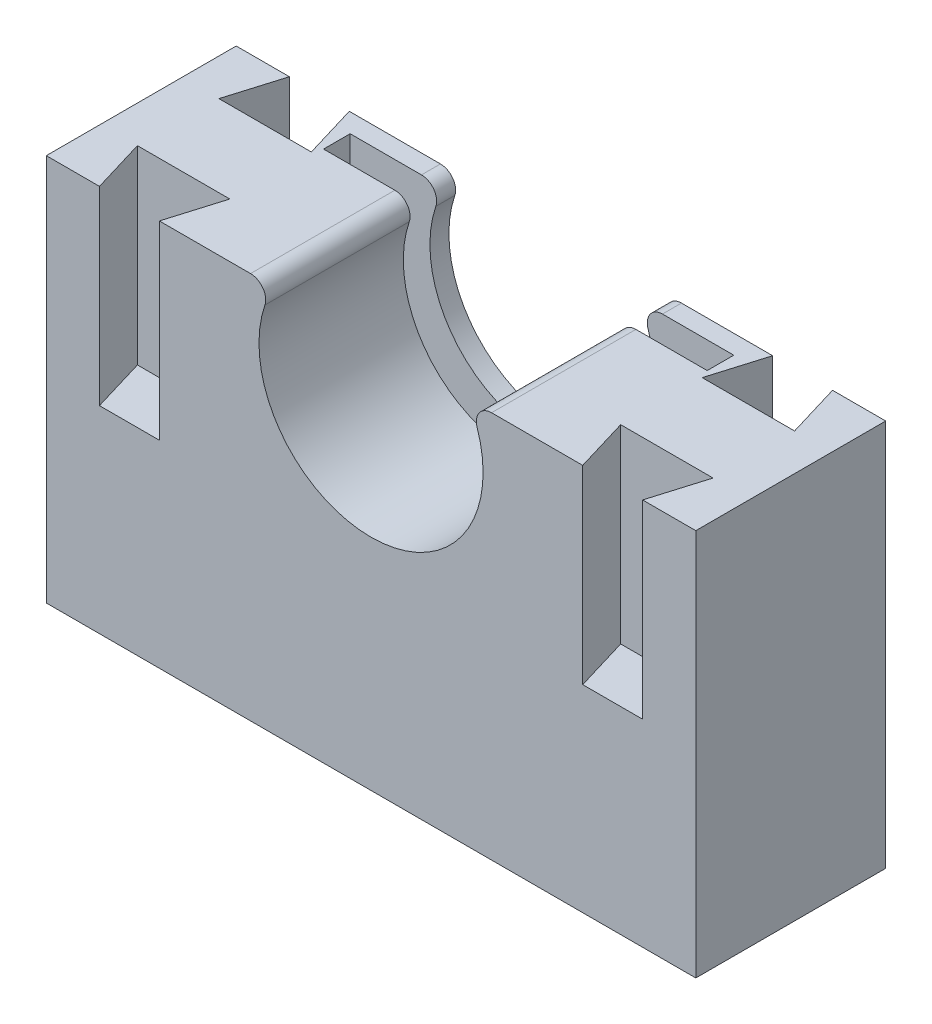
SolidWorks part; units mm, degrees
ref_plane "Front Plane" through (0, 0, 0) normal (0, 0, 1) x (1, 0, 0)
ref_plane "Top Plane" through (0, 0, 0) normal (0, 1, 0) x (1, 0, 0)
ref_plane "Right Plane" through (0, 0, 0) normal (1, 0, 0) x (0, 0, -1)
sketch "Sketch2" plane through (0, 0, 0) normal (0, 0, 1) x (1, 0, 0)
  line L0 (11.1505, 5.8899) -> (11.1505, -22.9851) construction
  line L1 (53.9005, 28.0149) -> (27.0147, 28.0149)
  line L2 (53.9005, 28.0149) -> (53.9005, -22.9851)
  line L3 (53.9005, -22.9851) -> (-31.5995, -22.9851)
  line L4 (-31.5995, 28.0149) -> (-31.5995, -22.9851)
  line L5 (-31.5995, 2.5149) -> (53.9005, 2.5149) construction
  line L6 (-4.7137, 28.0149) -> (-31.5995, 28.0149)
  line L7 (11.1505, 20.6399) -> (11.1505, -22.9851) construction
  line L8 (11.1505, 20.6399) -> (25.1204, 25.3731) construction
  line L9 (-3.5995, 20.6399) -> (25.9005, 20.6399) construction
  arc A0 (-2.8194, 25.3731) -> (25.1204, 25.3731) centre (11.1505, 20.6399) ccw
  arc A1 (-4.7137, 28.0149) -> (-2.8194, 25.3731) centre (-4.7137, 26.0149) cw
  arc A2 (27.0147, 28.0149) -> (25.1204, 25.3731) centre (27.0147, 26.0149) ccw
  dimension "D4" = 2
  dimension "D5" = 29.5
  dimension "D3" = 2
  dimension "D1" = 85.5
  dimension "D2" = 51
extrude "Boss-Extrude1" add sketch "Sketch2" along normal blind 25
sketch "Sketch5" plane through (0, 0, 25) normal (0, 0, 1) x (1, 0, 0)
  line L0 (11.1505, 5.8899) -> (11.1505, 1.4899) construction
  line L1 (-31.5995, -22.9851) -> (53.9005, -22.9851) construction
  line L2 (11.1505, 5.8899) -> (11.1505, 1.4899)
  line L3 (11.1505, -7.3101) -> (11.1505, -22.9851) construction
  arc A0 (-2.8194, 25.3731) -> (25.1204, 25.3731) centre (11.1505, 20.6399) ccw construction
  circle A1 centre (11.1505, -2.9101) radius 4.4
  dimension "D2" = 8.8
  dimension "D1" = 8.8
extrude "Cut-Extrude3" cut sketch "Sketch5" along normal blind 4.8 from surface at -25 contours A1 starting at face at (11.1505, 12.2907, 0)
sketch "Sketch6" plane through (0, 28.0149, 0) normal (0, 1, 0) x (1, 0, 0)
  line L0 (-24.5995, 0) -> (-26.7385, -7.1363)
  line L1 (-4.7137, 0) -> (-31.5995, 0) construction
  line L2 (-26.7385, -7.1363) -> (-14.5747, -7.1363)
  line L3 (-14.5747, -7.1363) -> (-16.7137, 0)
  line L4 (-31.5995, 0) -> (-24.5995, 0)
  line L5 (-16.7137, 0) -> (-4.7137, 0)
  line L6 (-31.5995, -25) -> (-24.5995, -25)
  line L7 (-4.7137, -25) -> (-31.5995, -25) construction
  line L8 (-24.5995, -25) -> (-26.7391, -17.8638)
  line L9 (-26.7391, -17.8638) -> (-14.5741, -17.8638)
  line L10 (-14.5741, -17.8638) -> (-16.7137, -25)
  line L11 (-16.7137, -25) -> (-4.7137, -25)
  line L12 (53.9005, 0) -> (46.9005, 0)
  line L13 (46.9005, 0) -> (49.0401, -7.1362)
  line L14 (49.0401, -7.1362) -> (36.8751, -7.1362)
  line L15 (36.8751, -7.1362) -> (39.0147, 0)
  line L16 (53.9005, 0) -> (27.0147, 0) construction
  line L17 (39.0147, 0) -> (27.0147, 0)
  line L18 (27.0147, -25) -> (39.0147, -25)
  line L19 (53.9005, -25) -> (27.0147, -25) construction
  line L20 (39.0147, -25) -> (36.8751, -17.8638)
  line L21 (36.8751, -17.8638) -> (49.0401, -17.8638)
  line L22 (49.0401, -17.8638) -> (46.9005, -25)
  line L23 (46.9005, -25) -> (53.9005, -25)
  line L24 (-31.5995, 0) -> (-31.5995, -25)
  line L27 (53.9005, 0) -> (53.9005, -25)
  line L28 (-4.7137, 0) -> (27.0147, 0)
  line L29 (27.0147, -25) -> (-4.7137, -25)
  dimension "D1" = 7
  dimension "D2" = 12
  dimension "D3" = 7.45
  dimension "D4" = 7.45
  dimension "D5" = 106.685
  dimension "D6" = 12.1639
  dimension "D7" = 7
  dimension "D8" = 12
  dimension "D9" = 7.45
  dimension "D10" = 7.45
  dimension "D11" = 106.69
  dimension "D12" = 12
  dimension "D13" = 7
  dimension "D14" = 7.45
  dimension "D15" = 7.45
  dimension "D16" = 106.69
  dimension "D17" = 12.165
  dimension "D18" = 12.165
  dimension "D19" = 12
  dimension "D20" = 7
  dimension "D21" = 7.45
  dimension "D22" = 106.69
  dimension "D23" = 7.45
extrude "Cut-Extrude4" cut sketch "Sketch6" against normal blind 25 flip side to cut
ref_plane "Plane1" through (0, 0, 2.5) normal (0, 0, -1) x (-1, 0, 0)
sketch "Sketch8" plane through (0, 0, 2.5) normal (0, 0, -1) x (-1, 0, 0)
  line L0 (-27.0147, 28.0149) -> (4.7137, 28.0149) construction
  line L1 (-11.1505, 28.0149) -> (-11.1505, -7.3101) construction
  line L2 (-36.4005, 2.9448) -> (14.0995, 2.9448)
  line L3 (-36.4005, 2.9448) -> (-36.4005, 28.0149)
  line L4 (-39.0147, 28.0149) -> (-27.0147, 28.0149) construction
  line L5 (-36.4005, 28.0149) -> (14.0995, 28.0149)
  line L6 (4.7137, 28.0149) -> (16.7137, 28.0149) construction
  line L7 (14.0995, 28.0149) -> (14.0995, 2.9448)
  circle A0 centre (-11.1505, -2.9101) radius 4.4 construction
  point P11 (-11.1505, 2.9448)
extrude "Cut-Extrude5" cut sketch "Sketch8" against normal blind 3.5
